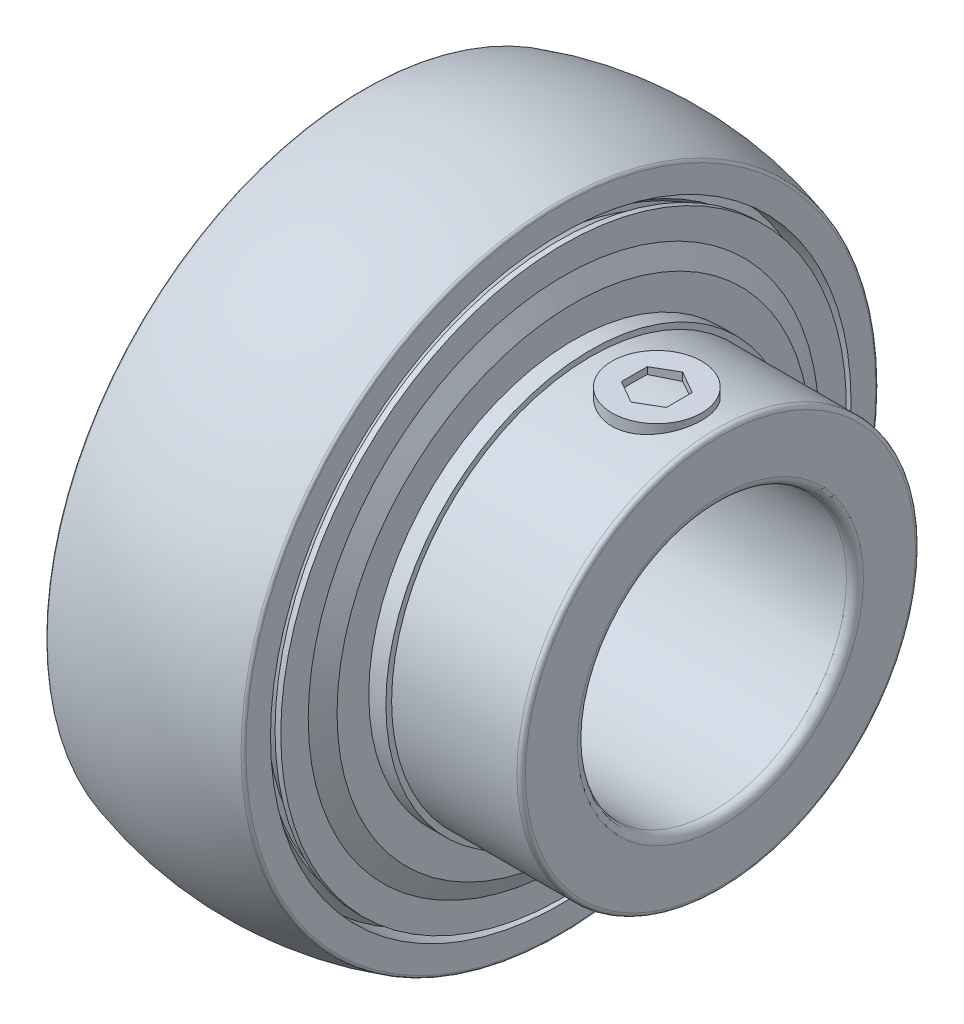
SolidWorks part; units mm, degrees
ref_plane "Alzado" through (0, 0, 0) normal (0, 0, 1) x (1, 0, 0)
ref_plane "Planta" through (0, 0, 0) normal (0, 1, 0) x (1, 0, 0)
ref_plane "Vista lateral" through (0, 0, 0) normal (1, 0, 0) x (0, 0, -1)
ref_plane "Plano1" through (0, 0, 0) normal (0, 0, 1) x (1, 0, 0)
sketch "Croquis1" plane through (0, 0, 0) normal (0, 0, 1) x (1, 0, 0)
  line L0 (-12.7, 13.8) -> (-12.7, 10.125)
  line L1 (-12.1, 9.525) -> (17.7, 9.525)
  line L2 (18.3, 10.125) -> (18.3, 13.8)
  line L3 (18, 14.1) -> (2.9547, 14.1)
  line L4 (-2.9547, 14.1) -> (-12.4, 14.1)
  line L5 (50, 0) -> (-50, 0) construction
  arc A0 (-12.7, 10.125) -> (-12.1, 9.525) centre (-12.1, 10.125) ccw
  arc A1 (17.7, 9.525) -> (18.3, 10.125) centre (17.7, 10.125) ccw
  arc A2 (18.3, 13.8) -> (18, 14.1) centre (18, 13.8) ccw
  arc A3 (2.9547, 14.1) -> (-2.9547, 14.1) centre (0, 16.75) cw
  arc A4 (-12.4, 14.1) -> (-12.7, 13.8) centre (-12.4, 13.8) ccw
revolve "Revolución1" add sketch "Croquis1" angle 360 about L5
ref_plane "Plano2" through (0, 9.525, 0) normal (0, 1, 0) x (1, 0, 0)
sketch "Croquis2" plane through (0, 9.525, 0) normal (0, 1, 0) x (1, 0, 0)
  line L0 (12.2125, -0.9165) -> (13.8, -1.8331)
  line L1 (13.8, -1.8331) -> (15.3875, -0.9165)
  line L2 (15.3875, -0.9165) -> (15.3875, 0.9165)
  line L3 (15.3875, 0.9165) -> (13.8, 1.8331)
  line L4 (13.8, 1.8331) -> (12.2125, 0.9165)
  line L5 (12.2125, 0.9165) -> (12.2125, -0.9165)
  circle A0 centre (13.8, 0) radius 3.175
extrude "Saliente-Extruir1" add sketch "Croquis2" along normal blind 5.0325
ref_plane "Plano3" through (0, -4.7625, -8.2489) normal (0, -0.5, -0.866) x (-1, 0, 0)
sketch "Croquis3" plane through (0, -4.7625, -8.2489) normal (0, -0.5, -0.866) x (-1, 0, 0)
  line L0 (-12.2125, 0.9165) -> (-13.8, 1.8331)
  line L1 (-13.8, 1.8331) -> (-15.3875, 0.9165)
  line L2 (-15.3875, 0.9165) -> (-15.3875, -0.9165)
  line L3 (-15.3875, -0.9165) -> (-13.8, -1.8331)
  line L4 (-13.8, -1.8331) -> (-12.2125, -0.9165)
  line L5 (-12.2125, -0.9165) -> (-12.2125, 0.9165)
  circle A0 centre (-13.8, 0) radius 3.175
extrude "Saliente-Extruir2" add sketch "Croquis3" along normal blind 5.0325
ref_plane "Plano4" through (0, 0, 0) normal (0, 0, 1) x (1, 0, 0)
sketch "Croquis4" plane through (0, 0, 0) normal (0, 0, 1) x (1, 0, 0)
  line L0 (4.5752, 20.5843) -> (4.5752, 18.0714)
  line L1 (4.5752, 18.0714) -> (5.114, 17.4095)
  line L2 (5.114, 17.4095) -> (5.114, 16.0857)
  line L3 (5.114, 16.0857) -> (4.5752, 15.4238)
  line L4 (4.5752, 15.4238) -> (4.5752, 14.7619)
  line L5 (4.5752, 14.7619) -> (4.7099, 14.1)
  line L6 (4.7099, 14.1) -> (5.114, 14.1)
  line L7 (5.114, 14.1) -> (4.9928, 14.6957)
  line L8 (4.9928, 14.6957) -> (6.1109, 14.6957)
  line L9 (6.1109, 14.6957) -> (6.1109, 17.45)
  line L10 (6.1109, 17.45) -> (4.873, 18.2945)
  line L11 (4.873, 18.2945) -> (4.9185, 18.3613)
  line L12 (4.9185, 18.3613) -> (6.1917, 17.4927)
  line L13 (6.1917, 17.4927) -> (6.1917, 14.4971)
  line L14 (6.1917, 14.4971) -> (6.5959, 14.4971)
  line L15 (6.5959, 14.4971) -> (6.5959, 17.7063)
  line L16 (6.5959, 17.7063) -> (7.2886, 16.9846)
  line L17 (7.5138, 16.4248) -> (7.5138, 14.1)
  line L18 (7.5138, 14.1) -> (9.1303, 14.1)
  line L19 (9.1303, 14.1) -> (9.1303, 14.5041)
  line L20 (9.1303, 14.5041) -> (7.9179, 14.5041)
  line L21 (7.9179, 14.5041) -> (7.9179, 16.75)
  line L22 (7.9179, 16.75) -> (7.2021, 18.073)
  line L23 (7.2021, 18.073) -> (7.2021, 20.0169)
  line L24 (7.2021, 20.0169) -> (6.7979, 20.0169)
  line L25 (6.7979, 20.0169) -> (6.7979, 18.073)
  line L26 (6.7979, 18.073) -> (5.7481, 18.2846)
  line L27 (5.7481, 18.2846) -> (4.9793, 18.809)
  line L28 (4.9793, 18.809) -> (4.9793, 19.9556)
  line L29 (4.9793, 19.9556) -> (5.3835, 19.4739)
  line L30 (5.3835, 19.4739) -> (5.6931, 19.7337)
  line L31 (5.6931, 19.7337) -> (4.9793, 20.5843)
  line L32 (4.8446, 20.719) -> (4.7099, 20.719)
  line L33 (7, 0) -> (-7, 0) construction
  arc A0 (7.2886, 16.9846) -> (7.5138, 16.4248) centre (6.7055, 16.4248) cw
  arc A1 (4.9793, 20.5843) -> (4.8446, 20.719) centre (4.8446, 20.5843) ccw
  arc A2 (4.7099, 20.719) -> (4.5752, 20.5843) centre (4.7099, 20.5843) ccw
revolve "Revolución2" add sketch "Croquis4" angle 360 about L33
ref_plane "Plano5" through (0, 0, 0) normal (0, 0, 1) x (1, 0, 0)
sketch "Croquis5" plane through (0, 0, 0) normal (0, 0, 1) x (1, 0, 0)
  line L0 (-7, 20.5419) -> (-5.0617, 20.5419)
  line L1 (-5.0617, 20.5419) -> (-4.9132, 20.6612)
  line L2 (-4.5639, 20.5321) -> (-4.4887, 20.1322)
  line L3 (-4.2391, 19.9252) -> (-2.4646, 19.9252)
  line L4 (2.4646, 19.9252) -> (4.2391, 19.9252)
  line L5 (4.4887, 20.1322) -> (4.5639, 20.5321)
  line L6 (4.9132, 20.6612) -> (5.0617, 20.5419)
  line L7 (5.0617, 20.5419) -> (7, 20.5419)
  line L8 (7, 20.5419) -> (7, 22.2856)
  line L9 (-7, 22.2856) -> (-7, 20.5419)
  line L10 (7, 0) -> (-7, 0) construction
  arc A0 (-4.9132, 20.6612) -> (-4.5639, 20.5321) centre (-4.7773, 20.4919) cw
  arc A1 (-4.4887, 20.1322) -> (-4.2391, 19.9252) centre (-4.2391, 20.1792) ccw
  arc A2 (-2.4646, 19.9252) -> (-2.3164, 19.9729) centre (-2.4646, 20.1792) ccw
  arc A3 (-2.3164, 19.9729) -> (2.3164, 19.9729) centre (0, 16.75) cw
  arc A4 (2.3164, 19.9729) -> (2.4646, 19.9252) centre (2.4646, 20.1792) ccw
  arc A5 (4.2391, 19.9252) -> (4.4887, 20.1322) centre (4.2391, 20.1792) ccw
  arc A6 (4.5639, 20.5321) -> (4.9132, 20.6612) centre (4.7773, 20.4919) cw
  arc A7 (7, 22.2856) -> (6.8584, 22.4769) centre (6.8, 22.2856) ccw
  arc A8 (6.8584, 22.4769) -> (-6.8584, 22.4769) centre (0, 0) ccw
  arc A9 (-6.8584, 22.4769) -> (-7, 22.2856) centre (-6.8, 22.2856) ccw
revolve "Revolución3" add sketch "Croquis5" angle 360 about L10
ref_plane "Plano6" through (0, 0, 0) normal (0, 0, 1) x (1, 0, 0)
sketch "Croquis6" plane through (0, 0, 0) normal (0, 0, 1) x (1, 0, 0)
  line L0 (-9.1303, 14.5041) -> (-9.1303, 14.1)
  line L1 (-9.1303, 14.1) -> (-7.5138, 14.1)
  line L2 (-7.5138, 14.1) -> (-7.5138, 16.4248)
  line L3 (-7.2886, 16.9846) -> (-6.5959, 17.7063)
  line L4 (-6.5959, 17.7063) -> (-6.5959, 14.4971)
  line L5 (-6.5959, 14.4971) -> (-6.1917, 14.4971)
  line L6 (-6.1917, 14.4971) -> (-6.1917, 17.4927)
  line L7 (-6.1917, 17.4927) -> (-4.9185, 18.3613)
  line L8 (-4.9185, 18.3613) -> (-4.873, 18.2945)
  line L9 (-4.873, 18.2945) -> (-6.1109, 17.45)
  line L10 (-6.1109, 17.45) -> (-6.1109, 14.6957)
  line L11 (-6.1109, 14.6957) -> (-4.9928, 14.6957)
  line L12 (-4.9928, 14.6957) -> (-5.114, 14.1)
  line L13 (-5.114, 14.1) -> (-4.7099, 14.1)
  line L14 (-4.7099, 14.1) -> (-4.5752, 14.7619)
  line L15 (-4.5752, 14.7619) -> (-4.5752, 15.4238)
  line L16 (-4.5752, 15.4238) -> (-5.114, 16.0857)
  line L17 (-5.114, 16.0857) -> (-5.114, 17.4095)
  line L18 (-5.114, 17.4095) -> (-4.5752, 18.0714)
  line L19 (-4.5752, 18.0714) -> (-4.5752, 20.5843)
  line L20 (-4.7099, 20.719) -> (-4.8446, 20.719)
  line L21 (-4.9793, 20.5843) -> (-5.6931, 19.7337)
  line L22 (-5.6931, 19.7337) -> (-5.3835, 19.4739)
  line L23 (-5.3835, 19.4739) -> (-4.9793, 19.9556)
  line L24 (-4.9793, 19.9556) -> (-4.9793, 18.809)
  line L25 (-4.9793, 18.809) -> (-5.7481, 18.2846)
  line L26 (-5.7481, 18.2846) -> (-6.7979, 18.073)
  line L27 (-6.7979, 18.073) -> (-6.7979, 20.0169)
  line L28 (-6.7979, 20.0169) -> (-7.2021, 20.0169)
  line L29 (-7.2021, 20.0169) -> (-7.2021, 18.073)
  line L30 (-7.2021, 18.073) -> (-7.9179, 16.75)
  line L31 (-7.9179, 16.75) -> (-7.9179, 14.5041)
  line L32 (-7.9179, 14.5041) -> (-9.1303, 14.5041)
  line L33 (7, 0) -> (-7, 0) construction
  arc A0 (-7.5138, 16.4248) -> (-7.2886, 16.9846) centre (-6.7055, 16.4248) cw
  arc A1 (-4.5752, 20.5843) -> (-4.7099, 20.719) centre (-4.7099, 20.5843) ccw
  arc A2 (-4.8446, 20.719) -> (-4.9793, 20.5843) centre (-4.8446, 20.5843) ccw
revolve "Revolución4" add sketch "Croquis6" angle 360 about L33
